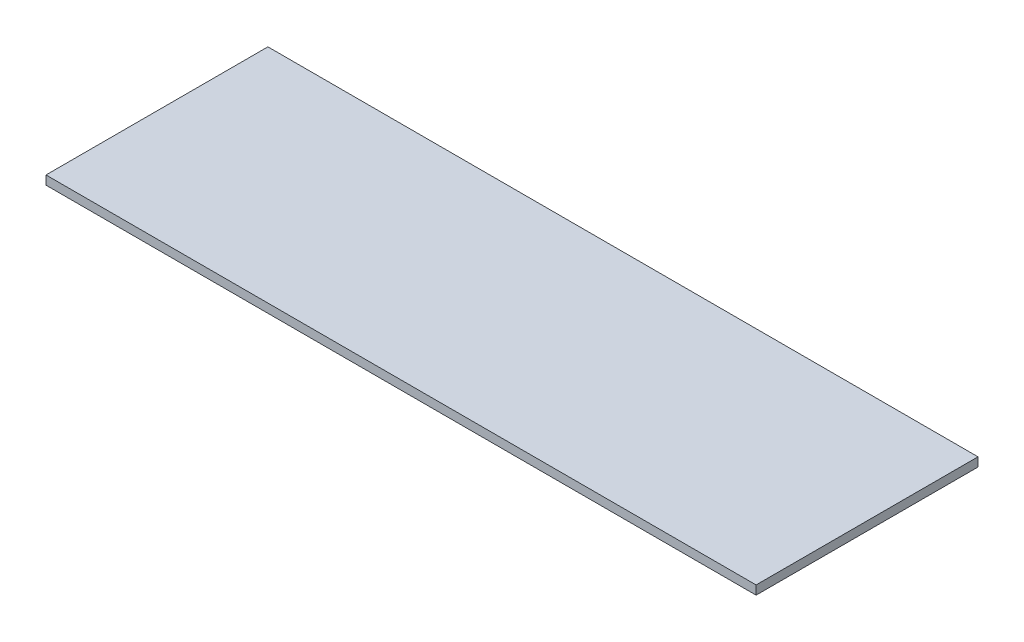
SolidWorks part; units mm, degrees
ref_plane "Front Plane" through (0, 0, 0) normal (0, 0, 1) x (1, 0, 0)
ref_plane "Top Plane" through (0, 0, 0) normal (0, 1, 0) x (1, 0, 0)
ref_plane "Right Plane" through (0, 0, 0) normal (1, 0, 0) x (0, 0, -1)
sketch "Sketch1" plane through (0, 0, 0) normal (0, 1, 0) x (1, 0, 0)
  line L1 (0, 0) -> (160, 0)
  line L2 (0, 0) -> (0, 50)
  line L3 (0, 50) -> (160, 50)
  line L4 (160, 0) -> (160, 50)
  dimension "D1" = 50
  dimension "D2" = 160
extrude "Boss-Extrude1" add sketch "Sketch1" along normal blind 2
